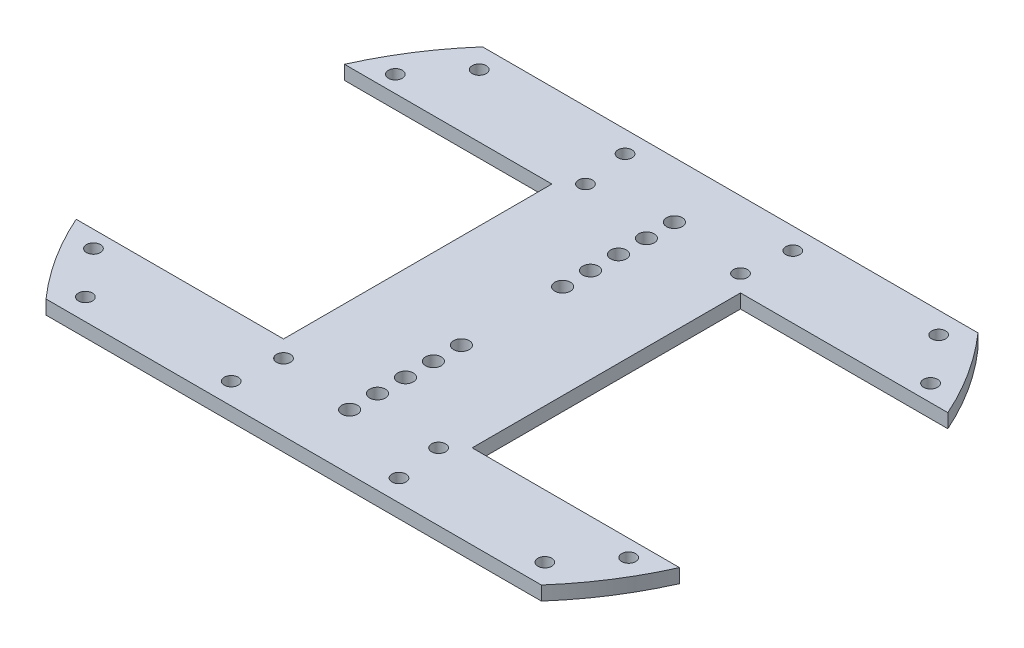
SolidWorks part; units mm, degrees
ref_plane "Front" through (0, 0, 0) normal (0, 0, 1) x (1, 0, 0)
ref_plane "Top" through (0, 0, 0) normal (0, 1, 0) x (1, 0, 0)
ref_plane "Right" through (0, 0, 0) normal (1, 0, 0) x (0, 0, -1)
sketch "Sketch1" plane through (0, 0, 0) normal (0, 1, 0) x (1, 0, 0)
  circle A0 centre (0, 0) radius 75
  circle A1 centre (0, 0) radius 75 construction
extrude "Boss-Extrude1" add sketch "Sketch1" along normal blind 3.175
sketch "Sketch2" plane through (0, 3.175, 0) normal (0, 1, 0) x (1, 0, 0)
  line L0 (-56.262, -49.5942) -> (56.262, -49.5942)
  line L1 (-56.262, 49.5942) -> (56.262, 49.5942)
  line L2 (-10, -49.5942) -> (10, -49.5942) construction
  circle A0 centre (0, 0) radius 75 construction
  arc A1 (-56.262, 49.5942) -> (56.262, 49.5942) centre (0, 0) cw
  arc A2 (-56.262, -49.5942) -> (56.262, -49.5942) centre (0, 0) ccw
extrude "Cut-Extrude1" cut sketch "Sketch2" against normal up to surface (3.175 mm away) up to face at (0, 0, 75)
sketch "Sketch3" plane through (0, 3.175, 0) normal (0, 1, 0) x (1, 0, 0)
  line L0 (-52.1803, 44.7298) -> (-19.05, 44.7298) construction
  line L1 (-19.05, 44.7298) -> (19.05, 44.7298) construction
  line L2 (19.05, 44.7298) -> (52.1803, 44.7298) construction
  line L3 (52.1803, 44.7298) -> (52.1803, -44.7298) construction
  line L4 (52.1803, -44.7298) -> (19.05, -44.7298) construction
  line L5 (19.05, -44.7298) -> (-19.05, -44.7298) construction
  line L6 (-19.05, -44.7298) -> (-52.1803, -44.7298) construction
  line L7 (-52.1803, -44.7298) -> (-52.1803, 44.7298) construction
  line L8 (-19.05, -44.7298) -> (-19.05, 44.7298) construction
  line L9 (19.05, 44.7298) -> (19.05, -44.7298) construction
  line L10 (-52.1803, 44.7298) -> (-56.262, 49.5942) construction
  line L11 (52.1803, 44.7298) -> (56.262, 49.5942) construction
  line L12 (52.1803, -44.7298) -> (56.262, -49.5942) construction
  line L13 (-52.1803, -44.7298) -> (-56.262, -49.5942) construction
  line L14 (56.262, -49.5942) -> (-56.262, -49.5942) construction
  circle A0 centre (0, 36.8942) radius 1.778
  circle A1 centre (0, 11.4942) radius 1.778
  circle A2 centre (0, 17.8442) radius 1.778
  circle A3 centre (0, 24.1942) radius 1.778
  circle A4 centre (0, 30.5442) radius 1.778
  circle A5 centre (0, -11.4942) radius 1.778
  circle A6 centre (0, -17.8442) radius 1.778
  circle A7 centre (0, -24.1942) radius 1.778
  circle A8 centre (0, -30.5442) radius 1.778
  circle A9 centre (0, -36.8942) radius 1.778
  circle A10 centre (-52.1803, -44.7298) radius 1.5875
  circle A11 centre (52.1803, -44.7298) radius 1.5875
  circle A12 centre (52.1803, 44.7298) radius 1.5875
  circle A13 centre (-52.1803, 44.7298) radius 1.5875
  circle A14 centre (-19.05, 44.7298) radius 1.5875
  circle A15 centre (-19.05, -44.7298) radius 1.5875
  circle A16 centre (19.05, -44.7298) radius 1.5875
  circle A17 centre (19.05, 44.7298) radius 1.5875
  dimension "D1" = 3.556
  dimension "D3" = 3.175
  dimension "D2" = 50
  dimension "D4" = 6.35
  dimension "D5" = 38.1
extrude "Cut-Extrude2" cut sketch "Sketch3" against normal up to surface (3.175 mm away) up to face at (0, 0, 0)
sketch "Sketch4" plane through (0, 3.175, 0) normal (0, 1, 0) x (1, 0, 0)
  line L0 (-60.7918, 34.29) -> (-17.6118, 34.29) construction
  line L1 (-17.6118, 34.29) -> (-17.6118, -34.29) construction
  line L2 (-17.6118, -34.29) -> (-60.7918, -34.29) construction
  line L3 (-60.7918, -34.29) -> (-60.7918, 34.29) construction
  line L4 (-64.6018, 38.1) -> (-13.8018, 38.1) construction
  line L5 (-13.8018, 38.1) -> (-13.8018, -38.1) construction
  line L6 (-13.8018, -38.1) -> (-64.6018, -38.1) construction
  line L7 (-64.6018, -38.1) -> (-64.6018, 38.1) construction
  line L8 (-64.6018, 0) -> (-60.7918, 0) construction
  line L9 (-39.2018, 38.1) -> (-39.2018, 34.29) construction
  line L10 (-39.2018, -34.29) -> (-39.2018, -38.1) construction
  line L11 (-17.6118, 0) -> (-13.8018, 0) construction
  line L12 (-75, 0) -> (-64.6018, 0) construction
  circle A0 centre (-60.7918, 34.29) radius 1.5875
  circle A1 centre (-17.6118, 34.29) radius 1.5875
  circle A6 centre (-17.6118, -34.29) radius 1.5875
  circle A7 centre (-60.7918, -34.29) radius 1.5875
  circle A8 centre (-52.1803, 44.7298) radius 1.5875 construction
  arc A9 (-56.262, 49.5942) -> (-56.262, -49.5942) centre (0, 0) ccw construction
  dimension "D1" = 43.18
  dimension "D2" = 68.58
  dimension "D3" = 50.8
extrude "Cut-Extrude3" cut sketch "Sketch4" against normal up to surface (3.175 mm away) up to face at (19.05, 0, -43.1423)
sketch "Sketch5" plane through (0, 3.175, 0) normal (0, 1, 0) x (1, 0, 0)
  line L0 (-68.5271, 30.48) -> (-21.4218, 30.48)
  line L1 (-21.4218, 30.48) -> (-21.4218, -30.48)
  line L2 (-21.4218, -30.48) -> (-68.5271, -30.48)
  line L3 (-17.6118, 34.29) -> (-17.6118, -34.29) construction
  line L4 (-60.7918, 34.29) -> (-17.6118, 34.29) construction
  arc A0 (-56.262, 49.5942) -> (-56.262, -49.5942) centre (0, 0) ccw construction
  arc A2 (-68.5271, 30.48) -> (-68.5271, -30.48) centre (0, 0) ccw
  dimension "D1" = 3.81
  dimension "D2" = 3.81
extrude "Cut-Extrude4" cut sketch "Sketch5" against normal up to surface (3.175 mm away) up to face at (-60.7918, 0, 35.8775)
mirror "Mirror1" about plane through (0, 0, 0) normal (1, 0, 0) of "Cut-Extrude4", "Cut-Extrude3"
